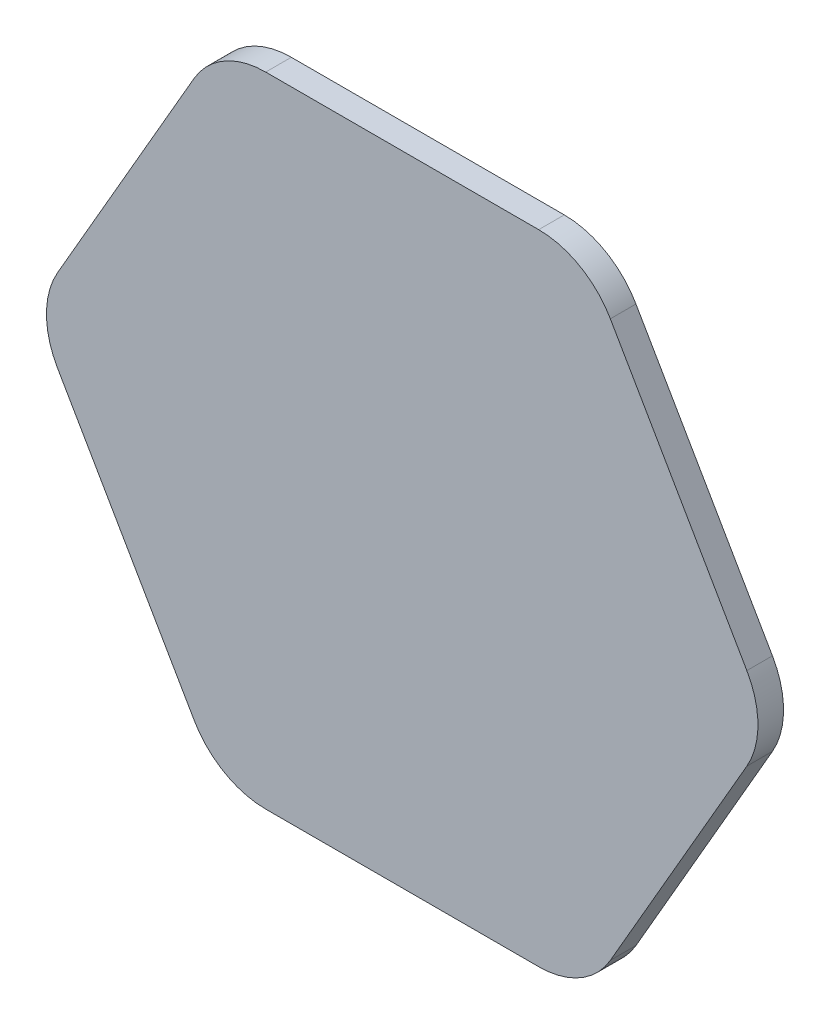
SolidWorks part; units mm, degrees
ref_plane "Front Plane" through (0, 0, 0) normal (0, 0, 1) x (1, 0, 0)
ref_plane "Top Plane" through (0, 0, 0) normal (0, 1, 0) x (1, 0, 0)
ref_plane "Right Plane" through (0, 0, 0) normal (1, 0, 0) x (0, 0, -1)
sketch "Sketch2" plane through (0, 0, 0) normal (0, 0, 1) x (1, 0, 0)
  line L1 (64.1346, 7.6987) -> (38.7346, 51.6928)
  line L2 (25.4, 59.3916) -> (-25.4, 59.3916)
  line L3 (-38.7346, 51.6928) -> (-64.1346, 7.6987)
  line L4 (-64.1346, -7.6987) -> (-38.7346, -51.6928)
  line L5 (-25.4, -59.3916) -> (25.4, -59.3916)
  line L6 (38.7346, -51.6928) -> (64.1346, -7.6987)
  circle A0 centre (0, 0) radius 59.3916 construction
  arc A1 (38.7346, 51.6928) -> (25.4, 59.3916) centre (25.4, 43.9941) ccw
  arc A2 (64.1346, 7.6987) -> (64.1346, -7.6987) centre (50.8, 0) cw
  arc A3 (25.4, -59.3916) -> (38.7346, -51.6928) centre (25.4, -43.9941) ccw
  arc A4 (-38.7346, -51.6928) -> (-25.4, -59.3916) centre (-25.4, -43.9941) ccw
  arc A5 (-64.1346, 7.6987) -> (-64.1346, -7.6987) centre (-50.8, 0) ccw
  arc A6 (-25.4, 59.3916) -> (-38.7346, 51.6928) centre (-25.4, 43.9941) ccw
  dimension "D1" = 50.8
  dimension "D2" = 59.3916
extrude "Boss-Extrude1" add sketch "Sketch2" along normal blind 4.7625
